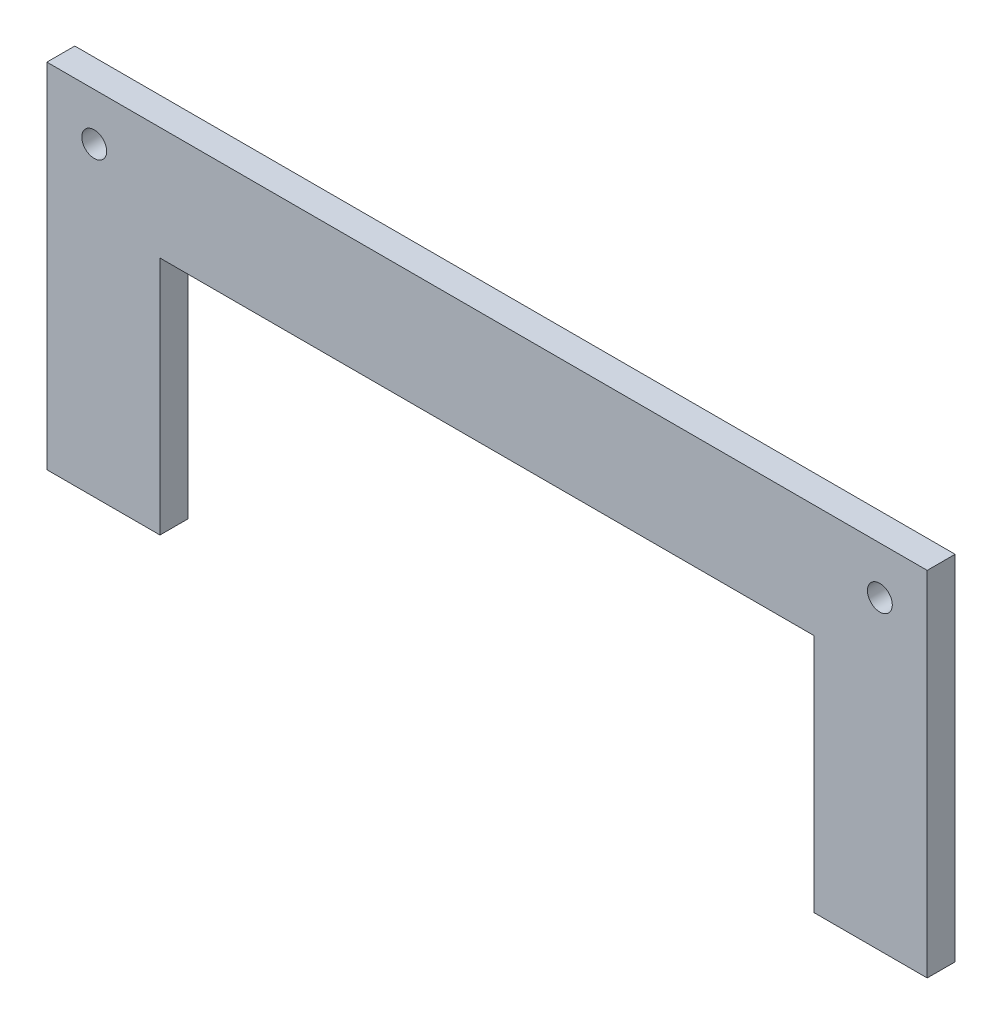
SolidWorks part; units mm, degrees
material "Maple"
ref_plane "Front Plane" through (0, 0, 0) normal (0, 0, 1) x (1, 0, 0)
ref_plane "Top Plane" through (0, 0, 0) normal (0, 1, 0) x (1, 0, 0)
ref_plane "Right Plane" through (0, 0, 0) normal (1, 0, 0) x (0, 0, -1)
sketch "Sketch1" plane through (0, 0, 0) normal (0, 0, 1) x (1, 0, 0)
  line L0 (-50, 0) -> (50, 0) construction
  line L1 (-50, 0) -> (-50, -40) construction
  line L2 (-50, -40) -> (-37.3, -40) construction
  line L3 (-37.3, -40) -> (-37.3, -12.7) construction
  line L4 (-37.3, -12.7) -> (37.3, -12.7) construction
  line L5 (37.3, -12.7) -> (37.3, -40) construction
  line L6 (37.3, -40) -> (50, -40) construction
  line L7 (50, -40) -> (50, 0) construction
  line L8 (-50, 0) -> (-44.6967, -5.3033) construction
  line L9 (0, 0) -> (0, -7.781) construction
  line L10 (50.085, -40.085) -> (50.085, 0.085)
  line L11 (-50.085, 0.085) -> (50.085, 0.085)
  line L12 (-50.085, 0.085) -> (-50.085, -40.085)
  line L13 (-50.085, -40.085) -> (-37.215, -40.085)
  line L14 (-37.215, -40.085) -> (-37.215, -12.785)
  line L15 (-37.215, -12.785) -> (37.215, -12.785)
  line L16 (37.215, -12.785) -> (37.215, -40.085)
  line L17 (37.215, -40.085) -> (50.085, -40.085)
  circle A0 centre (-44.6967, -5.3033) radius 1.415
  circle A1 centre (44.6967, -5.3033) radius 1.415
  point P4 (0, 0)
  dimension "D7" = 2.83
  dimension "D1" = 100
  dimension "D2" = 40
  dimension "D3" = 12.7
  dimension "D4" = 12.7
  dimension "D5" = 45
  dimension "D6" = 7.5
  dimension "D8" = 0.085
extrude "Boss-Extrude1" add sketch "Sketch1" along normal blind 3.175
equation "\"kerf\"= 0.17 / 2"
equation "\"D8@Sketch1\"= \"kerf\""
